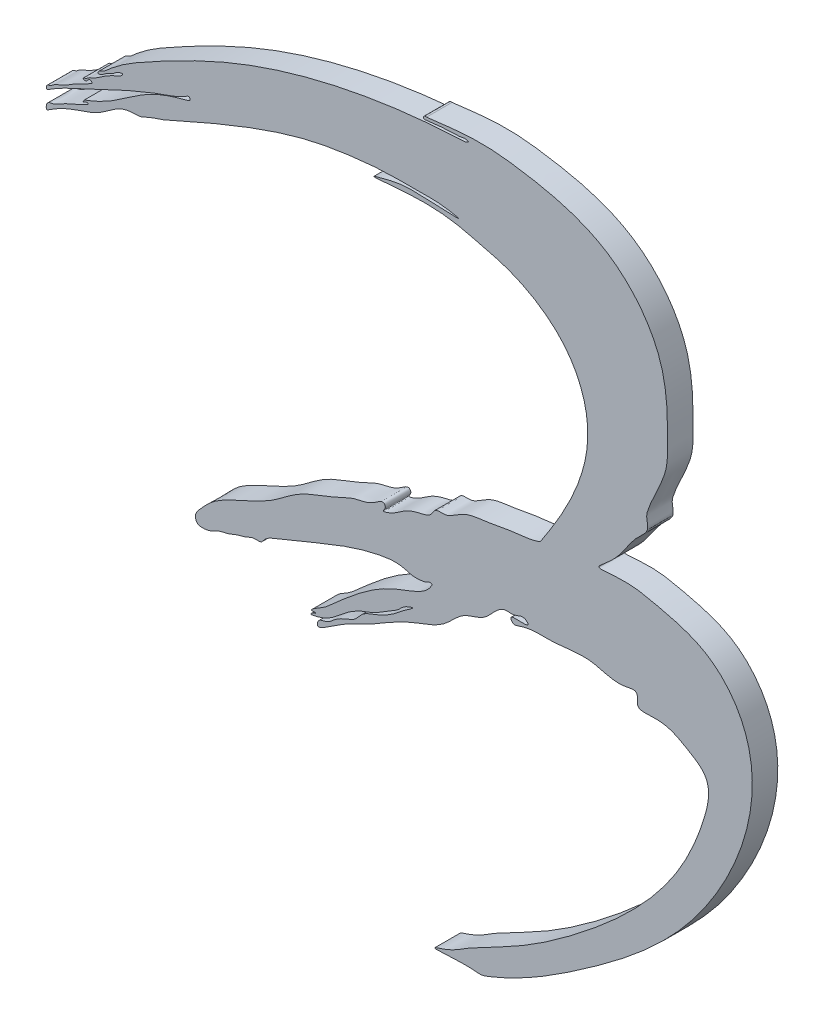
SolidWorks part; units mm, degrees
ref_plane "Plan de face" through (0, 0, 0) normal (0, 0, 1) x (1, 0, 0)
ref_plane "Plan de dessus" through (0, 0, 0) normal (0, 1, 0) x (1, 0, 0)
ref_plane "Plan de droite" through (0, 0, 0) normal (1, 0, 0) x (0, 0, -1)
sketch "Esquisse1" plane through (0, 0, 0) normal (0, 0, 1) x (1, 0, 0)
  spline S0 degree 3 poles (15.1995, 5.1983) (17.8218, 9.1834) (22.629, 16.9712) (18.5874, 27.5011) (12.5532, 30.8999) (6.4671, 32.3362) (3.4336, 33.4341) (-5.7705, 32.3249) (-1.5823, 33.386) (0.1181, 33.6057) (7.3028, 33.0777) (3.1417, 33.8324) (1.018, 33.6898) (-2.6472, 33.7993) (-7.4458, 33.3664) (-15.92, 31.9327) (-26.7016, 27.0577) (-29.296, 25.8997) (-30.7903, 25.4642) (-31.4982, 25.0133) (-32.3923, 24.9087) (-34.3862, 24.9651) (-36.0405, 22.8858) (-39.7119, 21.831) (-41.5025, 21.0173) (-42.8999, 20.06) (-42.8716, 21.123) (-41.9365, 21.0755) (-40.4553, 22.1003) (-39.3828, 22.3533) (-37.8227, 23.223) (-38.2288, 23.3432) (-38.6201, 22.9679) (-38.4533, 23.2593) (-38.3819, 23.3768) (-38.3787, 23.382) knots 0 0 0 0 0.034118 0.050236 0.068967 0.0735 0.095563 0.104191 0.107922 0.116908 0.126964 0.13031 0.137621 0.14482 0.154993 0.171422 0.207781 0.216896 0.21919 0.229442 0.232265 0.24613 0.386673 0.489154 0.601852 0.608768 0.628384 0.656974 0.686943 0.800375 0.806976 0.814482 0.827885 0.837106 0.837535 0.837535 0.837535 0.837535
  spline S1 degree 3 poles (-38.3787, 23.382) (-33.1515, 25.2717) (-32.8099, 27.8722) (-25.788, 29.498) (-26.1035, 29.9305) (-26.5076, 29.693) (-27.3605, 29.1655) (-30.1411, 28.2526) (-34.138, 26.5783) (-38.8592, 24.2229) (-41.3099, 23.1963) (-42.8741, 22.1504) (-42.8538, 22.7923) (-42.3483, 22.7941) (-41.8604, 23.2956) (-40.8146, 23.5681) (-39.6988, 24.4092) (-38.4615, 24.9111) (-37.8536, 25.3199) (-37.3581, 25.5581) (-37.7707, 25.8764) (-38.0009, 25.5363) (-38.2784, 25.3249) (-38.6207, 25.5704) (-38.1499, 25.6419) (-37.8695, 25.9445) (-37.0329, 26.2425) (-36.0328, 27.0208) (-34.8495, 27.655) (-34.0914, 27.9358) (-33.7846, 28.3326) (-34.5745, 28.2132) (-34.9215, 27.6802) (-35.9273, 27.3908) (-36.3189, 26.8955) (-36.8014, 26.8789) (-36.6709, 27.2903) (-36.1707, 27.3704) (-35.5899, 27.8735) (-34.0123, 29.2499) (-28.9885, 32.1303) (-17.4704, 37.9479) (-4.4959, 40.8022) (4.5739, 41.4198) (6.3768, 41.4981) (6.5733, 41.5353) (6.8169, 41.7185) (6.3448, 41.8831) (5.8229, 41.6652) (5.061, 41.7083) (4.7746, 41.6753) knots 0 0 0 0 0.134848 0.143034 0.144602 0.148639 0.15418 0.178068 0.234678 0.292201 0.330746 0.333193 0.337239 0.34163 0.346585 0.358072 0.373748 0.389768 0.396913 0.399366 0.402749 0.405986 0.410304 0.412056 0.415103 0.419095 0.426513 0.440579 0.458948 0.465949 0.467501 0.470952 0.480464 0.491217 0.499184 0.500837 0.502285 0.509316 0.515196 0.525664 0.573905 0.691977 0.923329 0.972552 0.974531 0.977935 0.97947 0.981332 0.988582 1 1 1 1
  spline S2 degree 3 poles (4.7746, 41.6753) (4.7608, 41.688) (2.6718, 41.5876) (1.6079, 41.3841) (1.4233, 41.4786) (1.5517, 41.7598) (1.6623, 41.7458) (1.8386, 41.7458) knots 0 0 0 0 0.789101 0.825842 0.866785 0.917494 1 1 1 1
  spline S3 degree 3 poles (1.8386, 41.7458) (4.2018, 42.0265) (7.9652, 42.5437) (15.3775, 41.6004) (23.7545, 39.6068) (30.2424, 31.0762) (30.1747, 24.5163) (30.1589, 19.1255) (28.3239, 16.3403) (27.5874, 13.8731) (28.1315, 12.6637) (26.4008, 11.2682) (25.0044, 9.1543) (23.827, 7.5822) (21.5115, 5.8199) (25.5807, 6.3348) (28.7122, 5.6298) (35.0285, 4.1972) (42.8999, -5.0804) (36.1886, -23.5666) (22.3914, -34.6135) (12.9895, -40.6186) (8.2569, -42.425) (6.9685, -42.2499) (5.5087, -42.2747) (1.7588, -42.5437) (4.7386, -41.7174) (7.034, -40.0834) (12.6536, -37.4554) (20.5245, -32.09) (29.375, -24.2253) (33.929, -16.0266) (35.582, -9.0711) (31.9442, -6.9301) (29.8199, -5.7225) (26.5194, -6.2396) (26.6818, -5.1157) (26.5712, -4.1715) (24.0625, -4.9801) (21.2176, -3.4734) (16.7834, -4.4644) (13.8816, -4.0913) (12.0495, -4.9092) (11.5299, -4.0131) (12.7327, -4.1071) (14.0634, -4.0949) (13.1513, -3.2082) (12.2507, -3.9554) (10.3479, -3.5331) (9.0529, -6.1015) (6.0086, -6.4903) (3.6986, -9.522) (-0.6008, -10.4794) (-5.0119, -13.5414) (-7.4743, -14.2333) (-11.1705, -17.0193) (-10.8685, -15.5992) (-9.7998, -15.622) (-8.9341, -14.7015) (-7.7947, -14.0917) (-6.4823, -13.6613) (-5.6756, -12.3758) (-3.8652, -11.8756) (-1.9819, -10.8063) (-1.0273, -9.9038) (0.675, -8.8077) (-0.9034, -9.3494) (-1.3983, -10.0762) (-2.8371, -10.8424) (-4.135, -11.8055) (-6.0084, -12.385) (-8.4162, -13.8051) (-9.5066, -15.3312) (-11.8413, -15.7007) (-11.5255, -15.3436) (-11.5189, -15.428) (-11.2219, -15.2913) knots 0 0 0 0 0.026687 0.041759 0.083493 0.118973 0.15054 0.156598 0.176995 0.180173 0.185825 0.19148 0.201603 0.213818 0.218107 0.223796 0.242243 0.2661 0.288782 0.36971 0.440445 0.490023 0.491708 0.496504 0.503315 0.512758 0.517467 0.527117 0.549028 0.582505 0.635087 0.675369 0.692164 0.702026 0.71711 0.724427 0.726292 0.728748 0.733278 0.748051 0.765921 0.779575 0.782783 0.784337 0.788152 0.791967 0.793474 0.798863 0.80206 0.813838 0.823241 0.834393 0.853281 0.871386 0.888313 0.896676 0.897774 0.902185 0.905809 0.911659 0.916426 0.920643 0.927543 0.936656 0.942844 0.946607 0.949758 0.954208 0.957935 0.967061 0.972246 0.979627 0.996876 0.997506 0.998263 1 1 1 1
  spline S4 degree 3 poles (-11.2219, -15.2913) (-11.1863, -15.1241) (-11.4298, -15.2538) (-11.7804, -15.2216) (-11.4148, -14.908) (-10.9893, -14.6309) (-9.9459, -14.058) (-8.5888, -12.7743) (-5.8824, -10.4216) (-2.3203, -7.9756) (1.7047, -6.9537) (2.4463, -5.6282) (2.5495, -5.457) (2.1035, -5.3513) (1.7771, -5.6716) (1.0112, -5.7648) (0.165, -5.8163) (-0.8908, -5.4242) (-2.0655, -5.3352) (-4.7045, -5.7145) (-8.0524, -6.773) (-12.2172, -8.5326) (-15.1627, -9.6736) (-17.0866, -10.5269) (-17.6045, -11.3772) (-18.5537, -11.1393) (-19.3592, -11.6661) (-20.4959, -11.8674) (-21.4207, -12.3769) (-22.5545, -12.5094) (-23.3745, -13.0606) (-24.2648, -13.259) (-25.189, -13.2096) (-25.4534, -12.2065) (-24.5632, -11.2199) (-23.1946, -9.6922) (-20.0785, -8.197) (-16.409, -6.6669) (-13.0439, -3.7172) (-9.5415, -2.7237) (-6.6245, -1.1425) (-4.743, -1.0704) (-3.2504, 0.283) (-2.9104, -0.4734) (-3.493, -1.0634) (-2.1908, -0.6232) (-1.548, -0.1837) (-0.3619, 0.6582) (0.9802, 1.049) (2.3634, 1.301) (2.8301, 2.4989) (3.9344, 2.2472) (5.0819, 2.7737) (6.527, 3.8751) (9.0479, 4.0356) (11.9604, 4.717) (14.0958, 4.774) (15.1995, 5.1983) knots 0 0 0 0 0.003835 0.005626 0.00865 0.013337 0.025485 0.043794 0.074034 0.138519 0.186487 0.188036 0.18927 0.191769 0.197818 0.204074 0.215307 0.224789 0.239449 0.252379 0.309643 0.350812 0.396295 0.411559 0.416285 0.42557 0.437284 0.446181 0.46202 0.470349 0.48205 0.492444 0.500051 0.507958 0.519114 0.539936 0.574207 0.626742 0.667092 0.713693 0.742758 0.767935 0.781266 0.784831 0.790075 0.797681 0.809789 0.823175 0.84057 0.856115 0.863527 0.876386 0.884884 0.903947 0.932867 0.962689 1 1 1 1
  point P34 (4.0244, -0.7154)
  point P92 (28.5168, 27.3292)
extrude "Boss.-Extru.1" add sketch "Esquisse1" along normal blind 3
